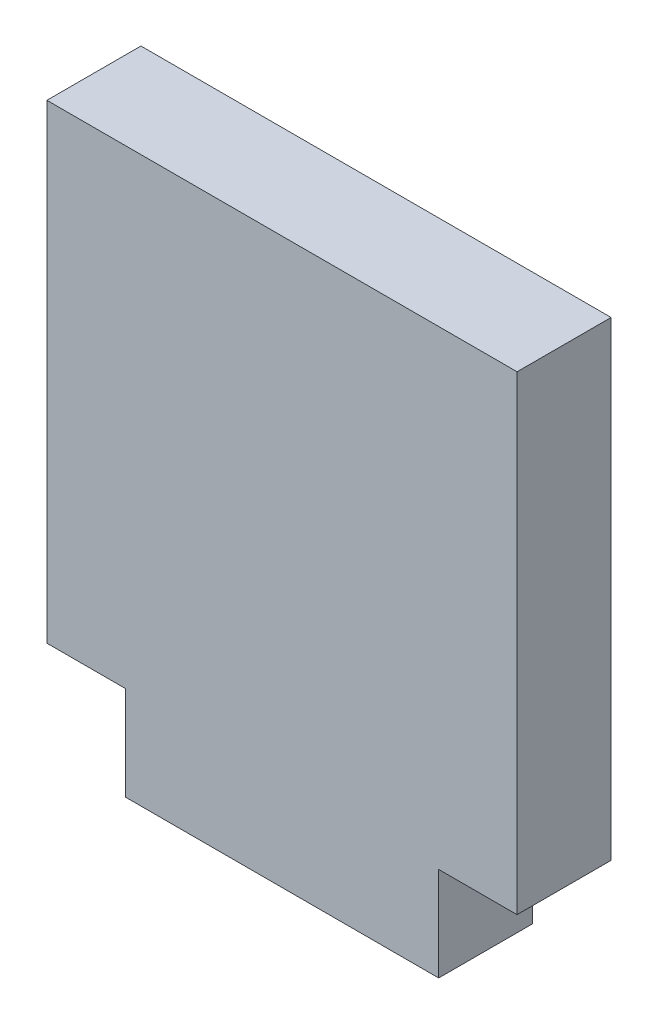
SolidWorks part; units mm, degrees
material "Acrylic (Medium-high impact)"
ref_plane "Front Plane" through (0, 0, 0) normal (0, 0, 1) x (1, 0, 0)
ref_plane "Top Plane" through (0, 0, 0) normal (0, 1, 0) x (1, 0, 0)
ref_plane "Right Plane" through (0, 0, 0) normal (1, 0, 0) x (0, 0, -1)
sketch "Sketch1" plane through (0, 0, 0) normal (0, 0, 1) x (1, 0, 0)
  line L14 (-7.5, 15) -> (7.5, 15)
  line L15 (-7.5, 15) -> (-7.5, 0)
  line L16 (-7.5, 0) -> (7.5, 0)
  line L17 (7.5, 15) -> (7.5, 0)
  line L18 (-5, 0) -> (5, 0)
  line L19 (-5, 0) -> (-5, -3)
  line L20 (-5, -3) -> (5, -3)
  line L21 (5, 0) -> (5, -3)
  point P8 (0, 15)
  point P9 (0, -3)
  dimension "D1" = 15
  dimension "D2" = 10
  dimension "D3" = 3
  dimension "D4" = 15
extrude "Boss-Extrude1" add sketch "Sketch1" along normal blind 3 contours L17 L14 L15 L16 | L21 L16 L19 L20
